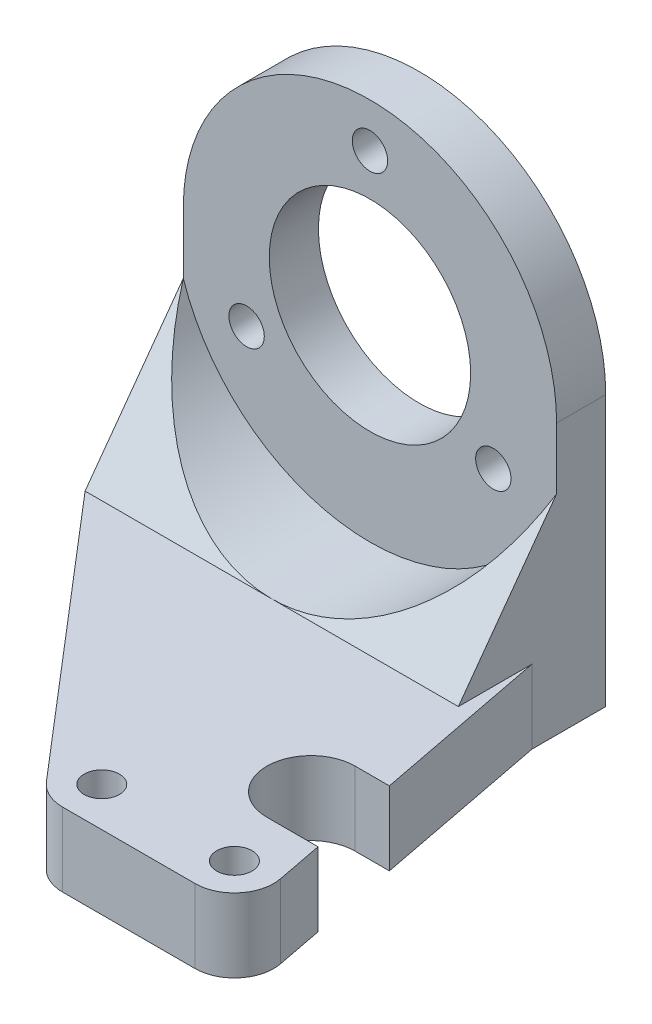
SolidWorks part; units mm, degrees
ref_plane "Front Plane" through (0, 0, 0) normal (0, 0, 1) x (1, 0, 0)
ref_plane "Top Plane" through (0, 0, 0) normal (0, 1, 0) x (1, 0, 0)
ref_plane "Right Plane" through (0, 0, 0) normal (1, 0, 0) x (0, 0, -1)
sketch "Sketch1" plane through (0, 0, 0) normal (0, 0, 1) x (1, 0, 0)
  line L0 (-19, 0) -> (-19, -27.5)
  line L1 (-19, -27.5) -> (19, -27.5)
  line L2 (19, -27.5) -> (19, 0)
  circle A0 centre (0, 0) radius 19
  circle A1 centre (0, 0) radius 10.25
  point P8 (0, 0)
  dimension "D1" = 38
  dimension "D2" = 20.5
  dimension "D3" = 27.5
extrude "Boss-Extrude1" add sketch "Sketch1" along normal blind 5 contours A0 A1 | A0 L0 L1 | A0 L1 L2
hole_wizard "M3 Clearance Hole1" positions "Sketch2" profile "Sketch4" hole size "M3" standard "ANSI Metric" end condition through all
sketch "Sketch2" plane through (0, 0, 5) normal (0, 0, 1) x (1, 0, 0)
  line L0 (0, -25.575) -> (0, 25.575) construction
  point P0 (0, 14.5)
  dimension "D1" = 14.5
sketch "Sketch4" plane through (0, 14.5, 5) normal (1, 0, 0) x (0, -1, 0)
  line L0 (0, 0) -> (0, 5)
  line L1 (0, 5) -> (1.8, 5)
  line L2 (1.8, 5) -> (1.8, 0)
  line L5 (1.8, 0) -> (0, 0)
  line L11 (0, -6.35) -> (0, 107.95) construction
  dimension "Thru Hole Dia." = 3.6
  dimension "Thru Hole Depth" = 5
pattern_circular "CirPattern1" count 3 over 360 about axis through (0, 0, 0) along (0, 0, 1) of "M3 Clearance Hole1"
sketch "Sketch6" plane through (0, 0, 0) normal (0, 0, 1) x (1, 0, 0)
  line L0 (-19, 0) -> (-19, -27.5) construction
  line L1 (-19, -27.5) -> (19, -27.5) construction
  line L2 (19, -27.5) -> (19, 0) construction
  line L3 (-19, 0) -> (-19, -27.5)
  line L4 (-19, -27.5) -> (19, -27.5)
  line L5 (19, -27.5) -> (19, 0)
  circle A2 centre (0, 0) radius 20
  circle A3 centre (0, 0) radius 20
  dimension "D1" = 1
extrude "Boss-Extrude2" add sketch "Sketch6" along normal blind 15 contours A3 L3 L4 L5
sketch "Sketch7" plane through (0, -27.5, 0) normal (0, -1, 0) x (1, 0, 0)
  line L0 (0, -25.575) -> (0, 25.575) construction
  line L1 (21.2, 44) -> (7.7, 44)
  line L2 (-19, 15) -> (4.6631, 42.6034)
  line L3 (19, 7.5) -> (25.1275, 39.2418)
  line L4 (19, 15) -> (19, 0) construction
  line L5 (19, 7.5) -> (19, 15)
  line L6 (19, 15) -> (-19, 15)
  line L8 (20.9, 0) -> (-20.9, 0) construction
  circle A0 centre (21.2, 40) radius 4
  circle A1 centre (7.7, 40) radius 4
  point P4 (8.3422, 25)
  point P15 (6.5494, 25)
  point P21 (0, 0)
  point P22 (7.7, 22)
  point P23 (7.7, 25)
  point P24 (7.7, 22)
  dimension "D4" = 7.7
  dimension "D2" = 8
  dimension "D1" = 13.5
  dimension "D3" = 40
extrude "Boss-Extrude3" add sketch "Sketch7" against normal blind 7.5
hole_wizard "M3 Clearance Hole2" positions "Sketch8" profile "Sketch9" hole size "M3" standard "ANSI Metric" end condition through all
sketch "Sketch8" plane through (0, -27.5, 0) normal (0, -1, 0) x (-1, 0, 0)
  point P0 (-21.2, -40)
  point P3 (-7.7, -40)
sketch "Sketch9" plane through (21.2, -27.5, 40) normal (1, 0, 0) x (0, 0, -1)
  line L0 (0, 0) -> (0, 46.5)
  line L1 (0, 46.5) -> (1.8, 46.5)
  line L2 (1.8, 46.5) -> (1.8, 0)
  line L5 (1.8, 0) -> (0, 0)
  line L11 (0, -6.35) -> (0, 107.95) construction
  dimension "Thru Hole Dia." = 3.6
  dimension "Thru Hole Depth" = 46.5
sketch "Sketch10" plane through (-19, 0, 0) normal (-1, 0, 0) x (0, 0, 1)
  line L0 (5, -6.245) -> (15, -20)
  line L1 (15, -20) -> (15, -6.245)
  line L2 (15, -6.245) -> (5, -6.245)
extrude "Cut-Extrude1" cut sketch "Sketch10" against normal through all
sketch "Sketch11" plane through (0, -27.5, 0) normal (0, -1, 0) x (1, 0, 0)
  line L0 (0, -8.25) -> (0, 8.25) construction
  line L1 (19, 34.5) -> (24.2121, 34.5)
  line L2 (19, 7.5) -> (25.1275, 39.2418) construction
  line L3 (19, 25.5) -> (22.4747, 25.5)
  line L4 (22.4747, 25.5) -> (24.2121, 34.5)
  arc A0 (19, 34.5) -> (19, 25.5) centre (19, 30) ccw
  circle A1 centre (7.7, 40) radius 1.8 construction
  dimension "D3" = 9
  dimension "D1" = 19
  dimension "D2" = 10
extrude "Cut-Extrude2" cut sketch "Sketch11" against normal through all
